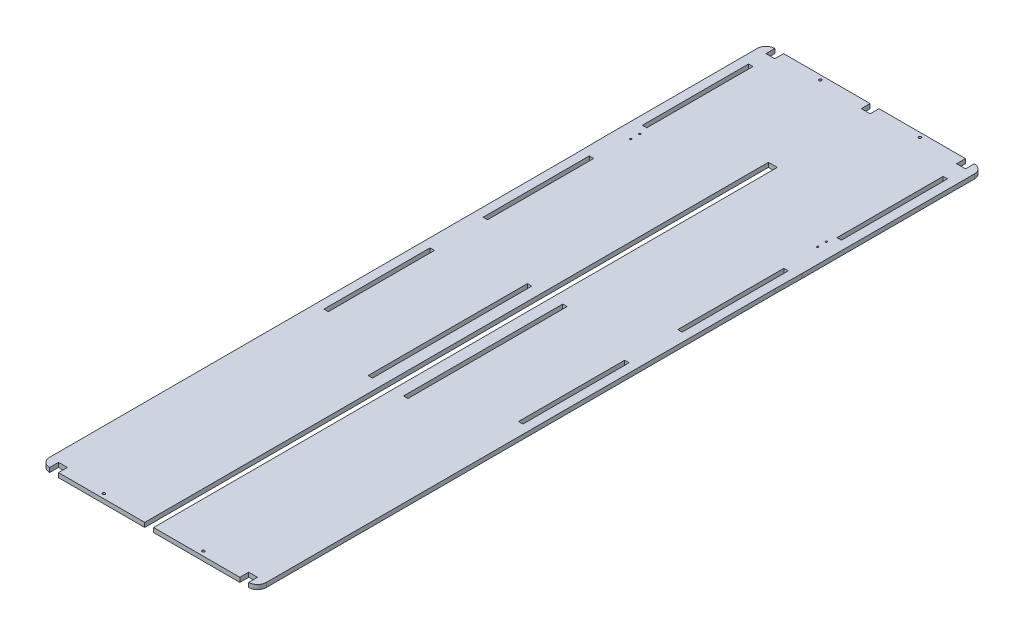
SolidWorks part; units mm, degrees
ref_plane "Front" through (0, 0, 0) normal (0, 0, 1) x (1, 0, 0)
ref_plane "Top" through (0, 0, 0) normal (0, 1, 0) x (1, 0, 0)
ref_plane "Right" through (0, 0, 0) normal (1, 0, 0) x (0, 0, -1)
sketch "Sketch2" plane through (0, 0, 0) normal (0, 1, 0) x (1, 0, 0)
  line L0 (122.5, 590) -> (122.5, -185) construction
  line L2 (0, 0) -> (0, 375)
  line L3 (0, 590) -> (245, 590)
  line L4 (245, -10) -> (245, 355)
  line L5 (10, 590) -> (10, -230) construction
  line L7 (117.5, -230) -> (117.5, 475)
  line L8 (117.5, 475) -> (127.5, 475)
  line L9 (127.5, -230) -> (127.5, 475)
  line L10 (117.5, -230) -> (127.5, 475) construction
  line L11 (117.5, 475) -> (127.5, -230) construction
  line L12 (10, -230) -> (15, -230)
  line L13 (15, -230) -> (15, 590) construction
  line L14 (235, 590) -> (235, -230) construction
  line L15 (235, -230) -> (230, -230)
  line L16 (230, -230) -> (230, 590) construction
  line L18 (0, 0) -> (0, -230)
  line L19 (245, -10) -> (245, -230)
  line L20 (0, -230) -> (117.5, -230)
  line L21 (127.5, -230) -> (245, -230)
  line L22 (-0.3, 405) -> (0, 375)
  line L23 (-0.3, 405) -> (-0.3, 590)
  line L24 (-0.3, 590) -> (0, 590)
  line L25 (10, 560) -> (15, 560)
  line L26 (245.3, 385) -> (245, 355)
  line L27 (245.3, 385) -> (245.3, 590)
  line L28 (245.3, 590) -> (245, 590)
  line L29 (10, 560) -> (10, 440)
  line L30 (10, 440) -> (15, 440)
  line L31 (15, 560) -> (15, 440)
  line L32 (15, 380) -> (10, 380)
  line L33 (15, 380) -> (15, 260)
  line L34 (15, 260) -> (10, 260)
  line L35 (10, 380) -> (10, 260)
  line L36 (10, 200) -> (15, 200)
  line L37 (10, 200) -> (10, 80)
  line L38 (10, 80) -> (15, 80)
  line L39 (15, 200) -> (15, 80)
  line L40 (230, 560) -> (235, 560)
  line L41 (230, 560) -> (230, 440)
  line L42 (230, 440) -> (235, 440)
  line L43 (235, 560) -> (235, 440)
  line L44 (230, 380) -> (235, 380)
  line L45 (230, 380) -> (230, 260)
  line L46 (230, 260) -> (235, 260)
  line L47 (235, 380) -> (235, 260)
  line L48 (230, 200) -> (235, 200)
  line L49 (230, 200) -> (230, 80)
  line L50 (230, 80) -> (235, 80)
  line L51 (235, 200) -> (235, 80)
  circle A0 centre (66.25, -225) radius 1.5
  circle A1 centre (178.75, -225) radius 1.5
  circle A2 centre (178.75, 585) radius 1.5
  circle A3 centre (66.25, 585) radius 1.5
  point P7 (122.5, 122.5)
  dimension "D24" = 3
  dimension "D27" = 3
  dimension "D29" = 51.25
  dimension "D30" = 3
  dimension "D34" = 3
  dimension "D1" = 245
  dimension "D2" = 820
  dimension "D3" = 115
  dimension "D4" = 10
  dimension "D5" = 590
  dimension "D6" = 10
  dimension "D7" = 5
  dimension "D8" = 10
  dimension "D9" = 5
  dimension "D10" = 30
  dimension "D11" = 120
  dimension "D12" = 60
  dimension "D13" = 0.3
  dimension "D14" = 30
  dimension "D15" = 30
  dimension "D16" = 120
  dimension "D17" = 60
  dimension "D18" = 120
  dimension "D19" = 120
  dimension "D20" = 60
  dimension "D21" = 120
  dimension "D22" = 60
  dimension "D23" = 120
  dimension "D25" = 5
  dimension "D26" = 51.25
  dimension "D28" = 5
  dimension "D31" = 5
  dimension "D32" = 51.25
  dimension "D33" = 5
  dimension "D35" = 51.25
extrude "Boss-Extrude1" add sketch "Sketch2" along normal blind 5
sketch "Sketch3" plane through (0, 5, 0) normal (0, 1, 0) x (1, 0, 0)
  line L0 (17, 510.3998) -> (17, 370) construction
  line L1 (0, -230) -> (0, 375) construction
  line L2 (-0.3, 590) -> (245.3, 590) construction
  line L3 (117.5, 475) -> (127.5, 475) construction
  line L4 (105, 220) -> (100, 220)
  line L5 (105, 220) -> (105, 40)
  line L6 (105, 40) -> (100, 40)
  line L7 (100, 220) -> (100, 40)
  line L8 (117.5, -230) -> (117.5, 475) construction
  circle A0 centre (17, 410) radius 1 construction
  circle A1 centre (17, 420) radius 1
  circle A2 centre (17, 430) radius 1
  circle A3 centre (17, 440) radius 1 construction
  dimension "D7" = 2
  dimension "D8" = 2
  dimension "D9" = 2
  dimension "D10" = 2
  dimension "D1" = 17
  dimension "D2" = 220
  dimension "D3" = 40
  dimension "D4" = 10
  dimension "D5" = 10
  dimension "D6" = 10
  dimension "D11" = 5
  dimension "D12" = 255
  dimension "D13" = 12.5
  dimension "D14" = 180
extrude "Cut-Extrude1" cut sketch "Sketch3" against normal blind 5
ref_plane "Plane1" through (122.5, 0, 0) normal (-1, 0, 0) x (0, 0, 1)
mirror "Mirror1" about plane through (122.5, 0, 0) normal (-1, 0, 0) of "Cut-Extrude1"
fillet "Fillet1" radius 10 4 edges at (245.3, 2.5, -590) (-0.3, 2.5, -590) (0, 2.5, 230) (245, 2.5, 230)
sketch "Sketch4" plane through (0, 5, 0) normal (0, 1, 0) x (1, 0, 0)
  line L0 (235.3, 590) -> (9.7, 590) construction
  line L1 (10, -230) -> (20, -230)
  line L2 (10, -230) -> (10, -220)
  line L3 (10, -220) -> (20, -220)
  line L4 (20, -230) -> (20, -220)
  line L5 (235, -230) -> (225, -230)
  line L6 (235, -230) -> (235, -220)
  line L7 (235, -220) -> (225, -220)
  line L8 (225, -230) -> (225, -220)
  line L9 (9.7, 590) -> (19.7, 590)
  line L10 (9.7, 590) -> (9.7, 580)
  line L11 (9.7, 580) -> (19.7, 580)
  line L12 (19.7, 590) -> (19.7, 580)
  line L13 (235.3, 590) -> (225.3, 590)
  line L14 (235.3, 590) -> (235.3, 580)
  line L15 (235.3, 580) -> (225.3, 580)
  line L16 (225.3, 590) -> (225.3, 580)
  line L17 (117.5, 590) -> (127.5, 590)
  line L18 (117.5, 590) -> (117.5, 580)
  line L19 (117.5, 580) -> (127.5, 580)
  line L20 (127.5, 590) -> (127.5, 580)
  point P26 (122.5, 590)
  point P27 (122.5, 590)
  dimension "D1" = 10
  dimension "D2" = 10
  dimension "D3" = 10
  dimension "D4" = 10
  dimension "D5" = 10
  dimension "D6" = 10
  dimension "D7" = 10
  dimension "D8" = 10
  dimension "D9" = 10
  dimension "D10" = 10
extrude "Cut-Extrude2" cut sketch "Sketch4" against normal blind 10
